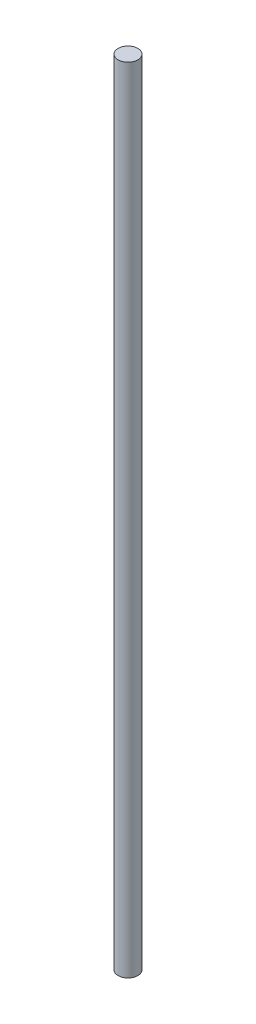
SolidWorks part; units mm, degrees
ref_plane "前视基准面" through (0, 0, 0) normal (0, 0, 1) x (1, 0, 0)
ref_plane "上视基准面" through (0, 0, 0) normal (0, 1, 0) x (1, 0, 0)
ref_plane "右视基准面" through (0, 0, 0) normal (1, 0, 0) x (0, 0, -1)
sketch "草图1" plane through (0, 0, 0) normal (0, 1, 0) x (1, 0, 0)
  circle A0 centre (0, 0) radius 5
extrude "凸台-拉伸1" add sketch "草图1" along normal blind 400
